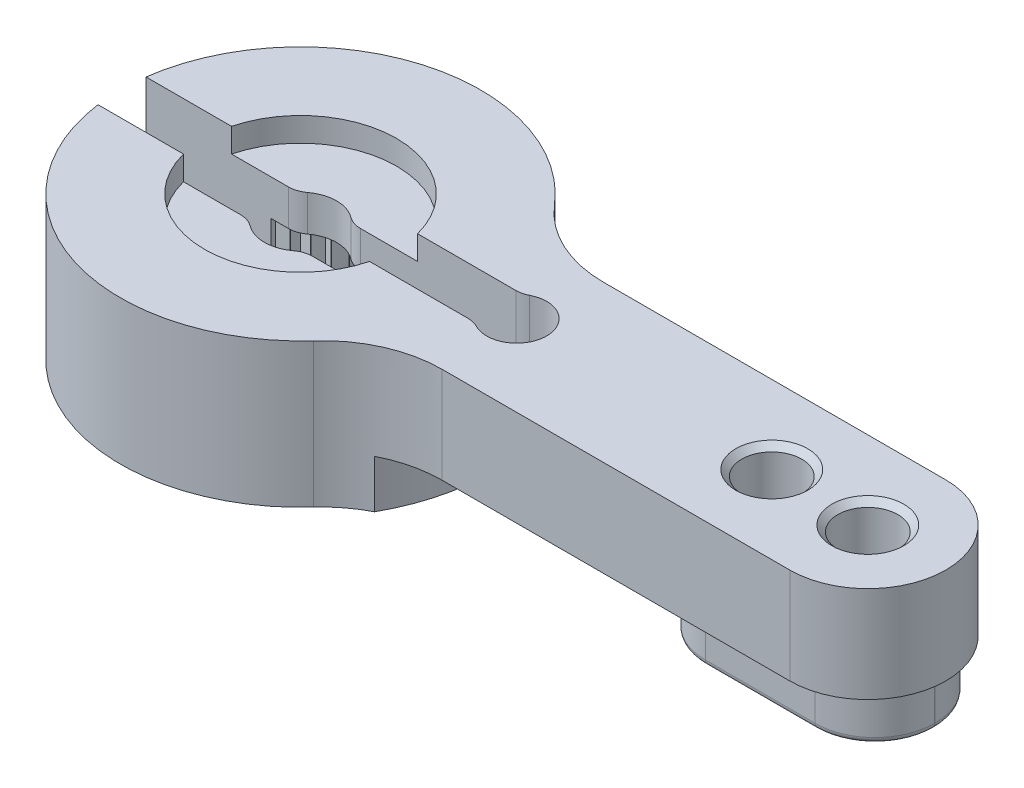
SolidWorks part; units mm, degrees
ref_plane "Front Plane" through (0, 0, 0) normal (0, 0, 1) x (1, 0, 0)
ref_plane "Top Plane" through (0, 0, 0) normal (0, 1, 0) x (1, 0, 0)
ref_plane "Right Plane" through (0, 0, 0) normal (1, 0, 0) x (0, 0, -1)
sketch "Sketch1" plane through (0, 0, 0) normal (0, 1, 0) x (1, 0, 0)
  line L1 (23.75, 3.122) -> (9.5017, 3.122)
  line L3 (23.75, -3.378) -> (9.2768, -3.378)
  arc A0 (5.701, 4.8732) -> (5.5661, -5.0268) centre (0, 0) ccw
  arc A1 (23.75, -3.378) -> (23.75, 3.122) centre (23.75, -0.128) ccw
  arc A2 (9.2768, -3.378) -> (5.5661, -5.0268) centre (9.2768, -8.378) ccw
  arc A3 (9.5017, 3.122) -> (5.701, 4.8732) centre (9.5017, 8.122) cw
  point P3 (3.89, -0.128)
  dimension "D1" = 15
  dimension "D2" = 5
  dimension "D3" = 3.25
  dimension "D4" = 23.75
extrude "Boss-Extrude1" add sketch "Sketch1" along normal mid plane 6
sketch "Sketch2" plane through (0, 3, 0) normal (0, 1, 0) x (1, 0, 0)
  circle A0 centre (23.75, -0.128) radius 1.25
  circle A1 centre (19.75, -0.128) radius 1.25
  dimension "D1" = 2.5
  dimension "D2" = 2.5
  dimension "D3" = 4
extrude "Cut-Extrude1" cut sketch "Sketch2" against normal blind 16
chamfer "Chamfer1" distance 0.25 angle 45 2 edges at (23.75, 3, 1.378) (19.75, 3, 1.378)
sketch "Sketch3" plane through (0, 3, 0) normal (0, 1, 0) x (1, 0, 0)
  circle A0 centre (0, 0) radius 4
  dimension "D1" = 8
extrude "Cut-Extrude2" cut sketch "Sketch3" against normal blind 1
sketch "Sketch4" plane through (0, 3, 0) normal (0, 1, 0) x (1, 0, 0)
  line L0 (-1.5, 1) -> (-9, 1)
  line L1 (7.9692, 1) -> (1.5, 1)
  line L3 (7.9692, -1) -> (1.5, -1)
  line L4 (-9, 1) -> (-9, -1)
  line L5 (-1.5, -1) -> (-9, -1)
  arc A0 (8.4273, -1.1111) -> (8.4273, 1.1111) centre (9, 0) ccw
  arc A1 (7.9692, -1) -> (8.4273, -1.1111) centre (7.9692, -2) cw
  arc A2 (7.9692, 1) -> (8.4273, 1.1111) centre (7.9692, 2) ccw
  arc A3 (-0.9, -1.2) -> (0.9, -1.2) centre (0, 0) ccw
  arc A4 (0.9, 1.2) -> (-0.9, 1.2) centre (0, 0) ccw
  arc A5 (-1.5, -1) -> (-0.9, -1.2) centre (-1.5, -2) cw
  arc A6 (0.9, -1.2) -> (1.5, -1) centre (1.5, -2) cw
  arc A7 (1.5, 1) -> (0.9, 1.2) centre (1.5, 2) cw
  arc A8 (-0.9, 1.2) -> (-1.5, 1) centre (-1.5, 2) cw
  point P0 (0, 0)
  point P19 (-1.118, -1)
  point P24 (1.118, 1)
  dimension "D3" = 2.5
  dimension "D1" = 1
  dimension "D4" = 3
  dimension "D5" = 1
  dimension "D2" = 2
extrude "Cut-Extrude3" cut sketch "Sketch4" against normal blind 11
sketch "Sketch5" plane through (0, -3, 0) normal (0, -1, 0) x (1, 0, 0)
  line L1 (24.0557, -4.372) -> (19.49, -4.372)
  line L2 (24.0557, 2.628) -> (19.49, 2.628)
  line L3 (26.5457, 0.138) -> (26.5457, 0.118)
  line L4 (24.0557, -2.372) -> (19.49, -2.372)
  line L5 (17, 0.138) -> (17, 0.118)
  line L8 (28.5457, 0.138) -> (28.5457, 0.118)
  line L9 (24.0557, 4.628) -> (19.49, 4.628)
  line L10 (19.49, 4.628) -> (6.5643, 4.628)
  line L11 (19.49, -4.372) -> (6.7375, -4.372)
  line L13 (15, 0.138) -> (15, 0.118) construction
  arc A2 (24.0557, -2.372) -> (26.5457, 0.118) centre (24.0557, 0.118) ccw
  arc A3 (26.5457, 0.138) -> (24.0557, 2.628) centre (24.0557, 0.138) ccw
  arc A4 (19.49, -2.372) -> (17, 0.118) centre (19.49, 0.118) cw
  arc A5 (19.49, 2.628) -> (17, 0.138) centre (19.49, 0.138) ccw
  arc A10 (24.0557, -4.372) -> (28.5457, 0.118) centre (24.0557, 0.118) ccw
  arc A11 (28.5457, 0.138) -> (24.0557, 4.628) centre (24.0557, 0.138) ccw
  arc A12 (19.49, 4.628) -> (15, 0.138) centre (19.49, 0.138) ccw construction
  arc A13 (19.49, -4.372) -> (15, 0.118) centre (19.49, 0.118) cw construction
  arc A14 (6.7375, -4.372) -> (6.5643, 4.628) centre (0, 0) ccw
  point P7 (21.75, 0.128)
  dimension "D3" = 2.49
  dimension "D4" = 2
extrude "Cut-Extrude4" cut sketch "Sketch5" against normal blind 2
fillet "Fillet1" radius 0.25 8 edges at (21.7728, -3, 2.628) (25.8164, -3, 1.8987) (26.5457, -3, 0.128) (25.8164, -3, -1.6427) (21.7728, -3, -2.372) (17.7293, -3, -1.6427) (17, -3, 0.128) (17.7293, -3, 1.8987)
sketch "Sketch6" plane through (0, -1, 0) normal (0, -1, 0) x (1, 0, 0)
  line L0 (17, 0.13) -> (17.001, 0.13)
  line L1 (23.75, 3.378) -> (9.2768, 3.378) construction
  line L2 (16.5723, 2.508) -> (10.6787, 2.508)
  line L4 (16.5723, -2.248) -> (10.6787, -2.248)
  line L8 (10.6787, 2.508) -> (9.4328, 2.508)
  line L9 (9.5017, -3.122) -> (23.75, -3.122) construction
  line L10 (16.5723, 2.508) -> (18.3723, 2.508)
  line L11 (16.5723, -2.248) -> (18.3654, -2.248)
  line L12 (10.6787, -2.248) -> (8.7549, -2.248)
  arc A1 (8.7549, -2.248) -> (9.4328, 2.508) centre (7.7683, 0.3189) ccw
  arc A3 (18.3723, 2.508) -> (18.3654, -2.248) centre (19.75, 0.128) ccw
  point P6 (13.6255, 0.13)
  dimension "D2" = 5.5
  dimension "D3" = 5.5
  dimension "D1" = 0.874
  dimension "1" = 0.87
extrude "Cut-Extrude5" cut sketch "Sketch6" against normal blind 3
sketch "Sketch7" plane through (0, -3, 0) normal (0, -1, 0) x (1, 0, 0)
  circle A0 centre (0, 0) radius 2.35
  dimension "D1" = 4.7
extrude "Cut-Extrude6" cut sketch "Sketch7" against normal blind 3.5
sketch "Sketch8" plane through (0, -3, 0) normal (0, -1, 0) x (1, 0, 0)
  line L0 (0, 0) -> (0, 4.5838) construction
  line L1 (0, 0) -> (0.6144, 4.6667)
  line L2 (0, 0) -> (-0.6513, 4.9472)
  line L4 (-0.3054, 2.32) -> (0.3054, 2.32)
  line L5 (0.3054, 2.32) -> (0, 2.849)
  line L6 (0, 2.849) -> (-0.3054, 2.32)
  circle A0 centre (0, 2.4963) radius 0.1763 construction
  arc M8 (-2.1266, 1) -> (2.1266, 1) centre (0, 0) cw
  dimension "D1" = 7.5
  dimension "D2" = 7.5
  dimension "D3" = 2.32
extrude "Cut-Extrude7" cut sketch "Sketch8" against normal blind 3.5 contours L5 L6 M8
pattern_circular "CirPattern1" count 24 over 360 about axis through (0, 0, 0) along (0, 1, 0) of "Cut-Extrude7"
